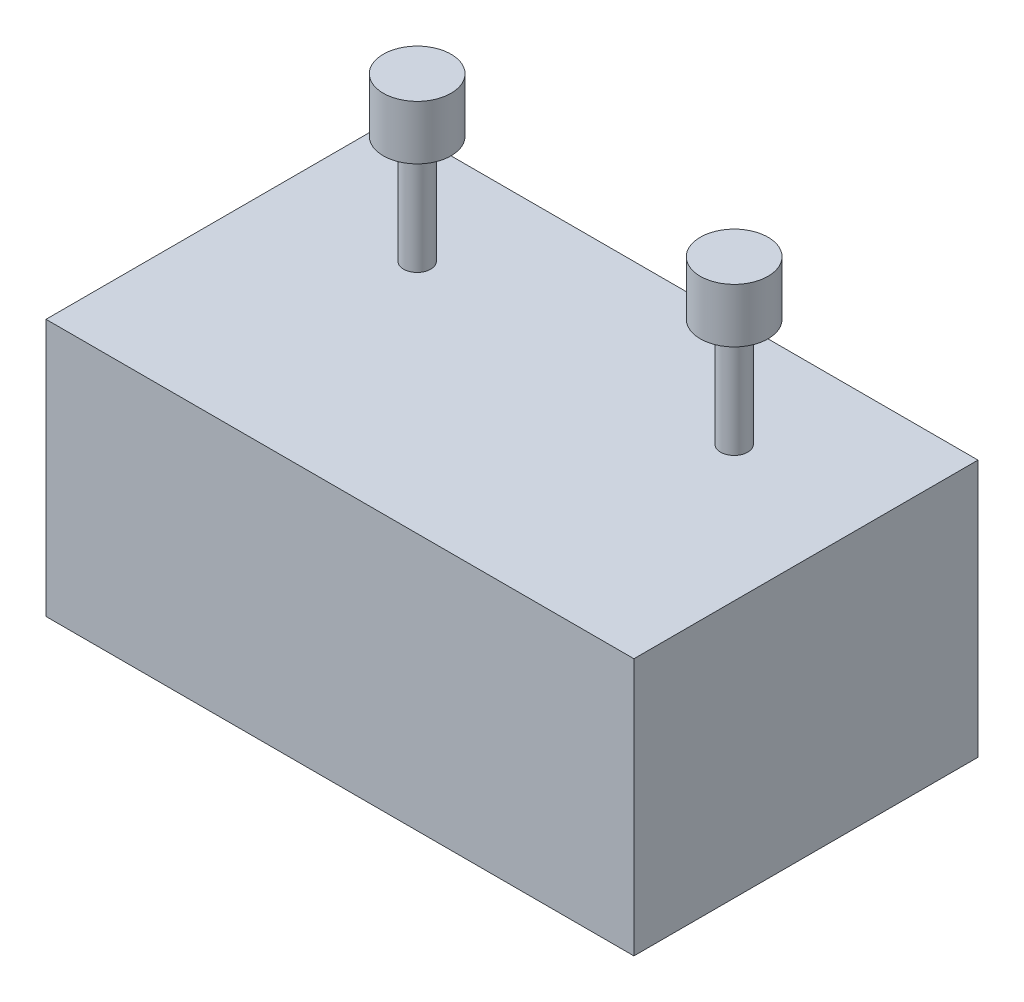
SolidWorks part; units mm, degrees
ref_plane "Front Plane" through (0, 0, 0) normal (0, 0, 1) x (1, 0, 0)
ref_plane "Top Plane" through (0, 0, 0) normal (0, 1, 0) x (1, 0, 0)
ref_plane "Right Plane" through (0, 0, 0) normal (1, 0, 0) x (0, 0, -1)
sketch "Sketch1" plane through (0, 0, 0) normal (0, 1, 0) x (1, 0, 0)
  line L1 (-108.5, -63.5) -> (108.5, -63.5)
  line L2 (-108.5, -63.5) -> (-108.5, 63.5)
  line L3 (-108.5, 63.5) -> (108.5, 63.5)
  line L4 (108.5, -63.5) -> (108.5, 63.5)
  line L5 (-108.5, -63.5) -> (108.5, 63.5) construction
  line L6 (-108.5, 63.5) -> (108.5, -63.5) construction
  point P0 (0, 0)
  dimension "D1" = 127
  dimension "D2" = 217
extrude "Boss-Extrude1" add sketch "Sketch1" along normal blind 95
sketch "Sketch2" plane through (0, 95, 0) normal (0, 1, 0) x (1, 0, 0)
  line L0 (0, 63.5) -> (0, -63.5) construction
  line L1 (108.5, 63.5) -> (-108.5, 63.5) construction
  line L2 (-108.5, -63.5) -> (108.5, -63.5) construction
  line L3 (-108.5, 63.5) -> (-108.5, -63.5) construction
  circle A0 centre (-58.5, 23.5) radius 5
  circle A1 centre (58.5, 23.5) radius 5
  dimension "D1" = 10
  dimension "D2" = 50
  dimension "D3" = 40
extrude "Boss-Extrude2" add sketch "Sketch2" along normal blind 40
sketch "Sketch3" plane through (0, 135, 0) normal (0, 1, 0) x (1, 0, 0)
  circle A0 centre (-58.5, 23.5) radius 12.5
  circle A1 centre (58.5, 23.5) radius 12.5
  dimension "D1" = 25
  dimension "D2" = 25
extrude "Boss-Extrude3" add sketch "Sketch3" along normal blind 20
